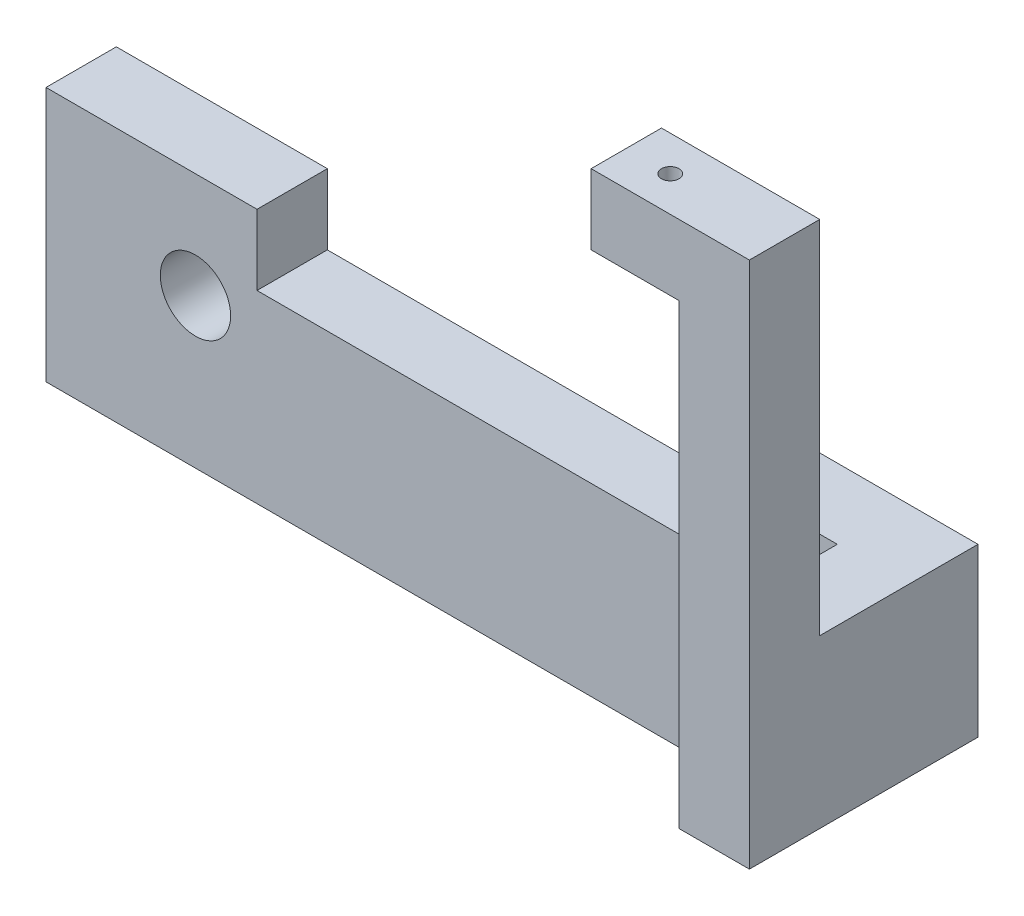
SolidWorks part; units mm, degrees
ref_plane "Front Plane" through (0, 0, 0) normal (0, 0, 1) x (1, 0, 0)
ref_plane "Top Plane" through (0, 0, 0) normal (0, 1, 0) x (1, 0, 0)
ref_plane "Right Plane" through (0, 0, 0) normal (1, 0, 0) x (0, 0, -1)
sketch "Sketch1" plane through (0, 0, 0) normal (0, 0, 1) x (1, 0, 0)
  line L0 (-96, 0) -> (-54.1209, 0)
  line L1 (-54.1209, 0) -> (-54.1209, 5)
  line L2 (-54.1209, 5) -> (-47, 5)
  line L3 (-47, 5) -> (-47, 14.5)
  line L7 (-59, 14.5) -> (-59, 10.5)
  line L8 (-59, 10.5) -> (-84, 10.5)
  line L9 (-84, 10.5) -> (-84, 14.5)
  line L11 (-84, 14.5) -> (-96, 14.5)
  line L13 (-96, 14.5) -> (-96, 0)
  line L14 (-51, 14.5) -> (-59, 14.5)
  line L16 (-47, 14.5) -> (-47, 35)
  line L17 (-47, 35) -> (-51, 35)
  line L19 (-51, 31) -> (-51, 14.5)
  line L20 (-51, 35) -> (-56, 35)
  line L22 (-51, 31) -> (-56, 31)
  line L23 (-56, 35) -> (-56, 31)
  circle A0 centre (-87.5, 8.5) radius 2
  circle A1 centre (-55.5, 8.5) radius 2
  dimension "D1" = 4
  dimension "D2" = 4
  dimension "D3" = 35
  dimension "D4" = 4
  dimension "D5" = 5
extrude "Boss-Extrude1" add sketch "Sketch1" along normal blind 13
sketch "Sketch5" plane through (0, 0, 13) normal (0, 0, 1) x (1, 0, 0)
  line L0 (-84, 14.5) -> (-96, 14.5)
  line L1 (-96, 14.5) -> (-96, 0)
  line L2 (-96, 0) -> (-54.1209, 0)
  line L3 (-54.1209, 0) -> (-54.1209, 5) construction
  line L4 (-96, 0) -> (-54.1209, 0) construction
  line L5 (-54.1209, 0) -> (-54.1209, 5)
  line L6 (-54.1209, 5) -> (-51, 5)
  line L7 (-54.1209, 5) -> (-47, 5) construction
  line L8 (-51, 5) -> (-51, 14.5)
  line L9 (-51, 14.5) -> (-59, 14.5)
  line L10 (-59, 14.5) -> (-59, 10.5)
  line L11 (-59, 10.5) -> (-84, 10.5)
  line L12 (-84, 10.5) -> (-84, 14.5)
extrude "Cut-Extrude2" cut sketch "Sketch5" against normal blind 9
sketch "Sketch6" plane through (0, 0, 0) normal (0, 0, -1) x (-1, 0, 0)
  line L0 (51, 31) -> (56, 31)
  line L1 (56, 31) -> (56, 35)
  line L2 (56, 35) -> (47, 35)
  line L3 (47, 35) -> (47, 14.5)
  line L4 (47, 5) -> (47, 35) construction
  line L5 (47, 14.5) -> (51, 14.5)
  line L6 (51, 14.5) -> (51, 31)
extrude "Cut-Extrude3" cut sketch "Sketch6" against normal blind 9
sketch "Sketch7" plane through (0, 31, 0) normal (0, -1, 0) x (-1, 0, 0)
  line L0 (56, -11) -> (51, -11) construction
  line L1 (56, -13) -> (56, -9) construction
  line L2 (51, -13) -> (51, -9) construction
  circle A0 centre (53.5, -11) radius 0.5
  dimension "D1" = 1
extrude "Cut-Extrude4" cut sketch "Sketch7" against normal up to surface (4 mm away) up to face at (-51.5, 35, 11)
